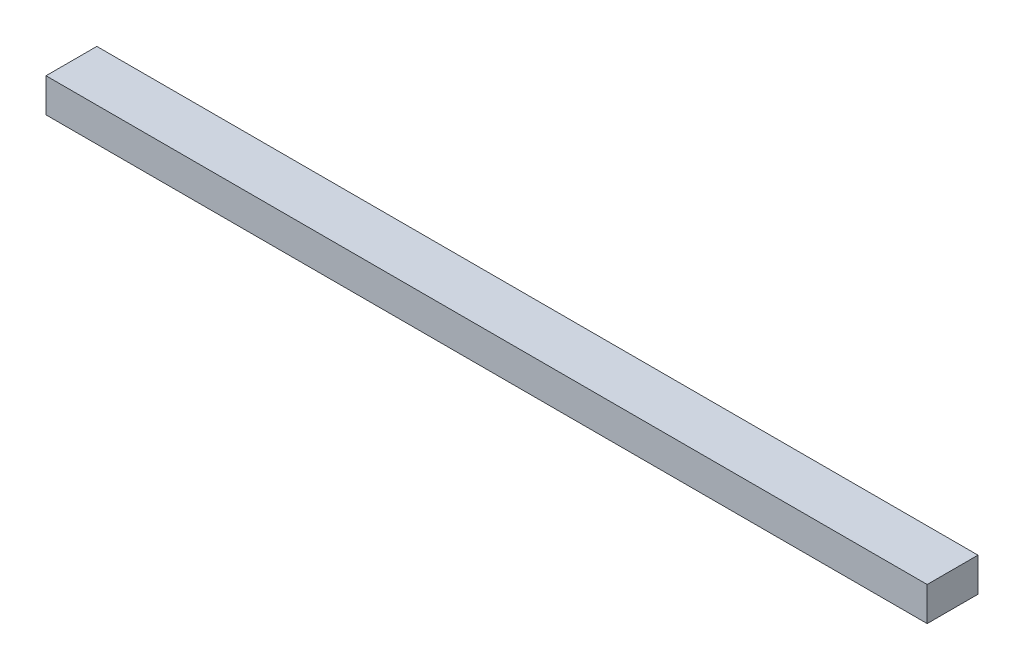
SolidWorks part; units mm, degrees
ref_plane "Front Plane" through (0, 0, 0) normal (0, 0, 1) x (1, 0, 0)
ref_plane "Top Plane" through (0, 0, 0) normal (0, 1, 0) x (1, 0, 0)
ref_plane "Right Plane" through (0, 0, 0) normal (1, 0, 0) x (0, 0, -1)
sketch "Sketch1" plane through (0, 0, 0) normal (0, 1, 0) x (1, 0, 0)
  line L1 (0, 0) -> (52, 0)
  line L2 (0, 0) -> (0, 3)
  line L3 (0, 3) -> (52, 3)
  line L4 (52, 0) -> (52, 3)
  dimension "D1" = 52
  dimension "D2" = 3
extrude "Boss-Extrude1" add sketch "Sketch1" along normal blind 2
